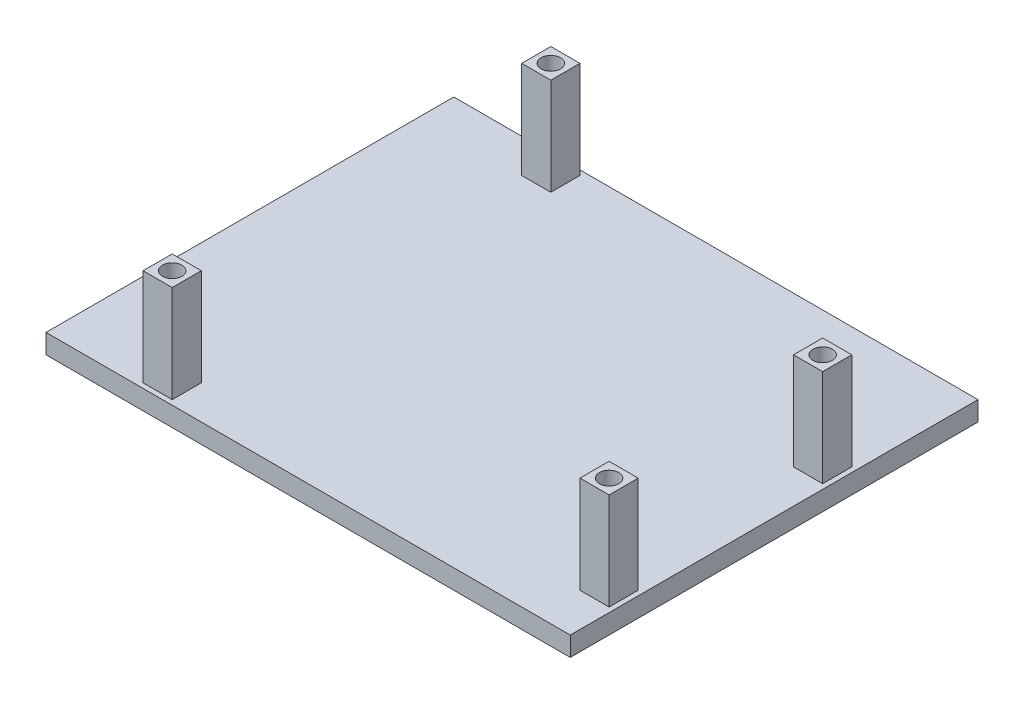
SolidWorks part; units mm, degrees
ref_plane "Front Plane" through (0, 0, 0) normal (0, 0, 1) x (1, 0, 0)
ref_plane "Top Plane" through (0, 0, 0) normal (0, 1, 0) x (1, 0, 0)
ref_plane "Right Plane" through (0, 0, 0) normal (1, 0, 0) x (0, 0, -1)
sketch "Sketch1" plane through (0, 0, 0) normal (0, 1, 0) x (1, 0, 0)
  line L1 (0, 0) -> (68.58, 0)
  line L2 (0, 0) -> (0, 53.34)
  line L3 (0, 53.34) -> (68.58, 53.34)
  line L4 (68.58, 0) -> (68.58, 53.34)
  dimension "D1" = 68.58
  dimension "D2" = 53.34
extrude "Boss-Extrude1" add sketch "Sketch1" along normal blind 2.54
sketch "Sketch2" plane through (0, 2.54, 0) normal (0, 1, 0) x (1, 0, 0)
  line L0 (0, 53.34) -> (0, 0) construction
  line L5 (12.065, 0.635) -> (15.875, 0.635)
  line L6 (12.065, 0.635) -> (12.065, 4.445)
  line L7 (12.065, 4.445) -> (15.875, 4.445)
  line L8 (15.875, 0.635) -> (15.875, 4.445)
  line L9 (12.065, 0.635) -> (15.875, 4.445) construction
  line L10 (12.065, 4.445) -> (15.875, 0.635) construction
  line L12 (0, 0) -> (68.58, 0) construction
  circle A1 centre (13.97, 2.54) radius 1.27
  point P0 (13.97, 2.54)
  point P11 (47.477, 0)
  dimension "D3" = 2.54
  dimension "D1" = 3.81
  dimension "D2" = 3.81
  dimension "D4" = 13.97
  dimension "D5" = 2.54
extrude "Boss-Extrude2" add sketch "Sketch2" along normal blind 12.7
sketch "Sketch3" plane through (0, 2.54, 0) normal (0, 1, 0) x (1, 0, 0)
  line L0 (0, 53.34) -> (0, 0) construction
  line L1 (13.335, 52.705) -> (17.145, 52.705)
  line L2 (13.335, 52.705) -> (13.335, 48.895)
  line L3 (13.335, 48.895) -> (17.145, 48.895)
  line L4 (17.145, 52.705) -> (17.145, 48.895)
  line L5 (13.335, 52.705) -> (17.145, 48.895) construction
  line L6 (13.335, 48.895) -> (17.145, 52.705) construction
  line L7 (68.58, 53.34) -> (0, 53.34) construction
  line L9 (64.135, 33.655) -> (67.945, 33.655)
  line L10 (64.135, 33.655) -> (64.135, 37.465)
  line L11 (64.135, 37.465) -> (67.945, 37.465)
  line L12 (67.945, 33.655) -> (67.945, 37.465)
  line L13 (64.135, 33.655) -> (67.945, 37.465) construction
  line L14 (64.135, 37.465) -> (67.945, 33.655) construction
  line L15 (64.135, 5.715) -> (67.945, 5.715)
  line L16 (64.135, 5.715) -> (64.135, 9.525)
  line L17 (64.135, 9.525) -> (67.945, 9.525)
  line L18 (67.945, 5.715) -> (67.945, 9.525)
  line L19 (64.135, 5.715) -> (67.945, 9.525) construction
  line L20 (64.135, 9.525) -> (67.945, 5.715) construction
  circle A0 centre (15.24, 50.8) radius 1.27
  circle A1 centre (66.04, 35.56) radius 1.27
  circle A2 centre (66.04, 7.62) radius 1.27
  point P0 (15.24, 50.8)
  point P11 (66.04, 35.56)
  point P18 (66.04, 7.62)
  dimension "D3" = 15.24
  dimension "D7" = 50.8
  dimension "D11" = 27.94
  dimension "D1" = 3.81
  dimension "D2" = 3.81
  dimension "D4" = 2.54
  dimension "D5" = 3.81
  dimension "D6" = 3.81
  dimension "D8" = 15.24
  dimension "D9" = 3.81
  dimension "D10" = 3.81
  dimension "D12" = 0
extrude "Boss-Extrude3" add sketch "Sketch3" along normal blind 12.7
